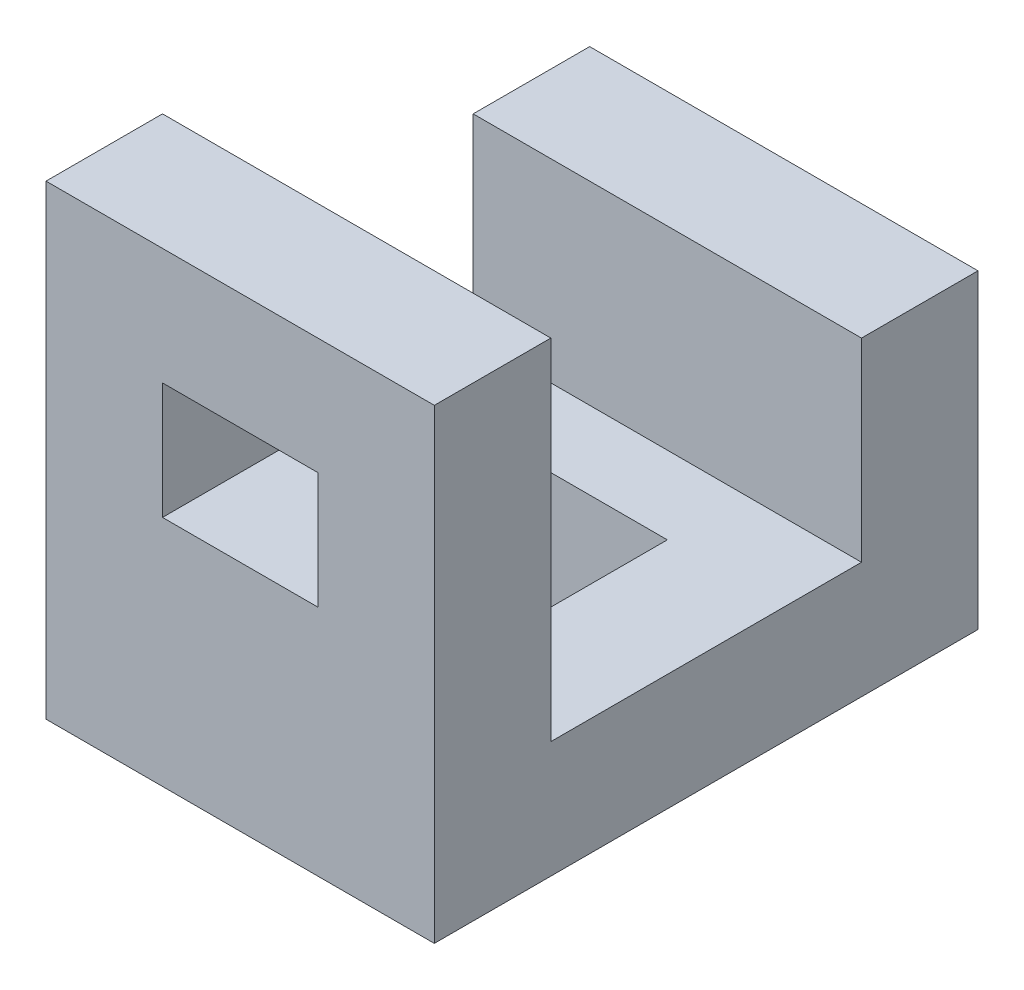
SolidWorks part; units mm, degrees
ref_plane "Front Plane" through (0, 0, 0) normal (0, 0, 1) x (1, 0, 0)
ref_plane "Top Plane" through (0, 0, 0) normal (0, 1, 0) x (1, 0, 0)
ref_plane "Right Plane" through (0, 0, 0) normal (1, 0, 0) x (0, 0, -1)
sketch "Sketch1" plane through (0, 0, 0) normal (0, 1, 0) x (1, 0, 0)
  line L0 (0, 0) -> (50, 0)
  line L1 (50, 0) -> (50, 70)
  line L2 (50, 70) -> (0, 70)
  line L3 (0, 70) -> (0, 0)
  dimension "D1" = 50
  dimension "D2" = 70
extrude "Boss-Extrude1" add sketch "Sketch1" along normal blind 60
sketch "Sketch2" plane through (0, 0, 0) normal (0, -1, 0) x (1, 0, 0)
  line L0 (15, -25) -> (15, -45)
  line L1 (15, -45) -> (35, -45)
  line L2 (35, -45) -> (35, -25)
  line L3 (35, -25) -> (15, -25)
  dimension "D1" = 20
  dimension "D2" = 20
  dimension "D3" = 25
  dimension "D4" = 15
extrude "Cut-Extrude1" cut sketch "Sketch2" against normal blind 60
sketch "Sketch3" plane through (0, 0, 0) normal (-1, 0, 0) x (0, 0, 1)
  line L1 (-15, 60) -> (-15, 15)
  line L2 (-70, 60) -> (0, 60) construction
  line L3 (-15, 15) -> (-55, 15)
  line L4 (-55, 15) -> (-55, 40)
  line L5 (-55, 40) -> (-70, 40)
  line L6 (-70, 60) -> (-70, 0) construction
  line L7 (-70, 40) -> (-70, 60)
  line L8 (-70, 60) -> (-15, 60)
  dimension "D1" = 15
  dimension "D2" = 55
  dimension "D3" = 25
  dimension "D4" = 45
extrude "Cut-Extrude2" cut sketch "Sketch3" against normal blind 50
sketch "Sketch4" plane through (0, 0, 0) normal (0, 0, 1) x (1, 0, 0)
  line L0 (35, 45) -> (15, 45)
  line L1 (15, 45) -> (15, 30)
  line L2 (15, 30) -> (35, 30)
  line L3 (35, 30) -> (35, 45)
  dimension "D1" = 30
  dimension "D2" = 15
  dimension "D3" = 15
  dimension "D4" = 20
  dimension "D5" = 15
extrude "Cut-Extrude3" cut sketch "Sketch4" against normal blind 50
